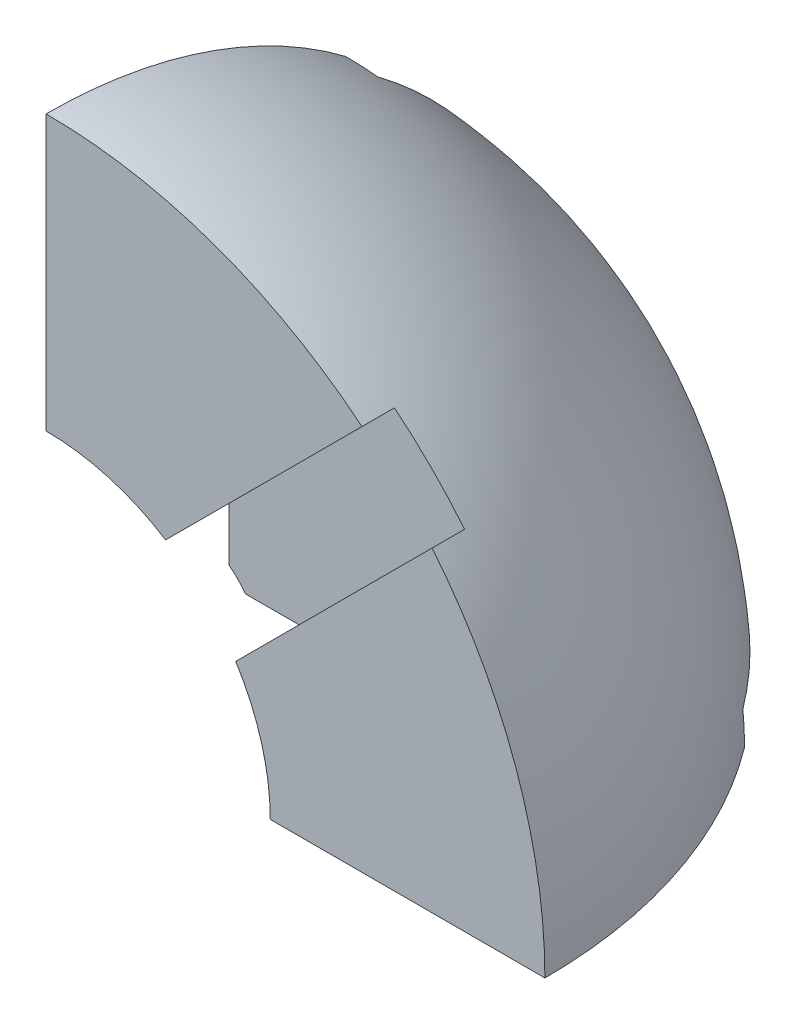
SolidWorks part; units mm, degrees
ref_plane "Front Plane" through (0, 0, 0) normal (0, 0, 1) x (1, 0, 0)
ref_plane "Top Plane" through (0, 0, 0) normal (0, 1, 0) x (1, 0, 0)
ref_plane "Right Plane" through (0, 0, 0) normal (1, 0, 0) x (0, 0, -1)
sketch "Sketch4" plane through (0, 0, 0) normal (0, 1, 0) x (1, 0, 0)
  line L1 (0, 0) -> (15, 0)
  line L2 (0, 0) -> (0, 15)
  arc A0 (0, 15) -> (15, 0) centre (0, 0) cw
  dimension "D1" = 15
revolve "Revolve1" add sketch "Sketch4" angle 90 about L1
sketch "Sketch5" plane through (0, 0, 0) normal (0, 0, 1) x (1, 0, 0)
  line L2 (0, 0) -> (0, 15) construction
  line L3 (0, 0) -> (15, 0) construction
  circle A0 centre (3, 3) radius 2.5
  dimension "D1" = 5
  dimension "D2" = 3
  dimension "D3" = 3
extrude "Cut-Extrude3" cut sketch "Sketch5" against normal blind 13
sketch "Sketch6" plane through (0, 0, 0) normal (-1, 0, 0) x (0, 0, 1)
  line L0 (0, 0) -> (0, 15) construction
  line L1 (0, 0) -> (-15, 0) construction
  circle A0 centre (-3, 3) radius 2.5
  dimension "D3" = 5
  dimension "D1" = 3
  dimension "D2" = 3
extrude "Cut-Extrude4" cut sketch "Sketch6" against normal blind 13
sketch "Sketch7" plane through (0, 0, 0) normal (0, -1, 0) x (1, 0, 0)
  line L0 (0, 0) -> (15, 0) construction
  line L1 (0, 0) -> (0, -15) construction
  circle A0 centre (3, -3) radius 2.5
  dimension "D2" = 5
  dimension "D1" = 3
  dimension "D3" = 3
extrude "Cut-Extrude5" cut sketch "Sketch7" against normal blind 13
sketch "Sketch8" plane through (0, 0, 0) normal (0, 0, 1) x (1, 0, 0)
  line L0 (0, 0) -> (0, 15) construction
  line L1 (0, 0) -> (15, 0) construction
  arc A1 (0, 6.7426) -> (6.7426, 0) centre (0, 0) cw
  circle A2 centre (3, 3) radius 2.5 construction
revolve "Cut-Revolve14" cut sketch "Sketch8" angle 90 about axis through (0, 0, 0) along (0, 1, 0)
sketch "Sketch9" plane through (0, 0, 0) normal (0, 0, 1) x (1, 0, 0)
  line L3 (9.5, 11.6082) -> (11.6082, 9.5)
  line L8 (9.5, 11.6082) -> (-1.0541, 1.0541)
  line L9 (11.6082, 9.5) -> (1.0541, -1.0541)
  line L10 (-1.0541, 1.0541) -> (1.0541, -1.0541)
  line L11 (6.7426, 0) -> (15, 0) construction
  line L12 (0, 6.7426) -> (0, 15) construction
  arc A1 (15, 0) -> (0, 15) centre (0, 0) ccw construction
  circle A5 centre (0, 0) radius 15
  circle A6 centre (0, 0) radius 6.7426
  point P13 (0, 0)
  arc M4 (4.7678, 4.7678) -> (6.7426, 0) centre (0, 0) cw
  arc M6 (15, 0) -> (0, 15) centre (0, 0) ccw
  arc M8 (0, 6.7426) -> (4.7678, 4.7678) centre (0, 0) cw
  dimension "D1" = 2.9814
  dimension "D2" = 13.4853
  dimension "D3" = 30
  dimension "D4" = 9.5
  dimension "D5" = 9.5
extrude "Cut-Extrude20" cut sketch "Sketch9" against normal blind 1 contours L3 M6 | L9 L3 L8 M8 M4 | L8 L10 L9 M4 M8
sketch "Sketch10" plane through (0, 0, 0) normal (-1, 0, 0) x (0, 0, 1)
  line L0 (-12, 9) -> (-9, 12)
  line L1 (-12, 9) -> (-1.5, -1.5)
  line L2 (-9, 12) -> (1.5, 1.5)
  line L3 (-1.5, -1.5) -> (1.5, 1.5)
  line L4 (-6.7426, 0) -> (-15, 0) construction
  line L5 (0, 6.7426) -> (0, 15) construction
  circle A0 centre (0, 0) radius 15
  arc A1 (-12, 9) -> (-9, 12) centre (0, 0) ccw
  point P5 (0, 0)
  arc M7 (-6.7426, 0) -> (-4.7678, 4.7678) centre (0, 0) cw
  arc M8 (-4.7678, 4.7678) -> (0, 6.7426) centre (0, 0) cw
  arc M10 (0, 15) -> (-15, 0) centre (0, 0) ccw
  dimension "D2" = 30
  dimension "D1" = 9
  dimension "D3" = 9
extrude "Cut-Extrude24" cut sketch "Sketch10" against normal blind 1 contours L2 L0 L1 M7 M8 | L0 M10 | L1 L3 L2 M8 M7
sketch "Sketch11" plane through (0, 0, 0) normal (0, -1, 0) x (1, 0, 0)
  line L0 (9, -12) -> (12, -9)
  line L1 (9, -12) -> (-1.5, -1.5)
  line L2 (12, -9) -> (1.5, 1.5)
  line L3 (-1.5, -1.5) -> (1.5, 1.5)
  line L4 (0, -6.7426) -> (0, -15) construction
  line L5 (6.7426, 0) -> (15, 0) construction
  circle A0 centre (0, 0) radius 15
  arc A1 (12, -9) -> (9, -12) centre (0, 0) ccw
  point P3 (0, 0)
  point P6 (0, 0)
  arc M7 (6.7426, 0) -> (4.7678, -4.7678) centre (0, 0) cw
  arc M8 (4.7678, -4.7678) -> (0, -6.7426) centre (0, 0) cw
  arc M10 (0, -15) -> (15, 0) centre (0, 0) ccw
  dimension "D1" = 30
  dimension "D2" = 9
  dimension "D3" = 9
extrude "Cut-Extrude25" cut sketch "Sketch11" against normal blind 1 contours L0 M10 | L0 L2 L1 M7 M8 | L3 L1 L2 M8 M7
